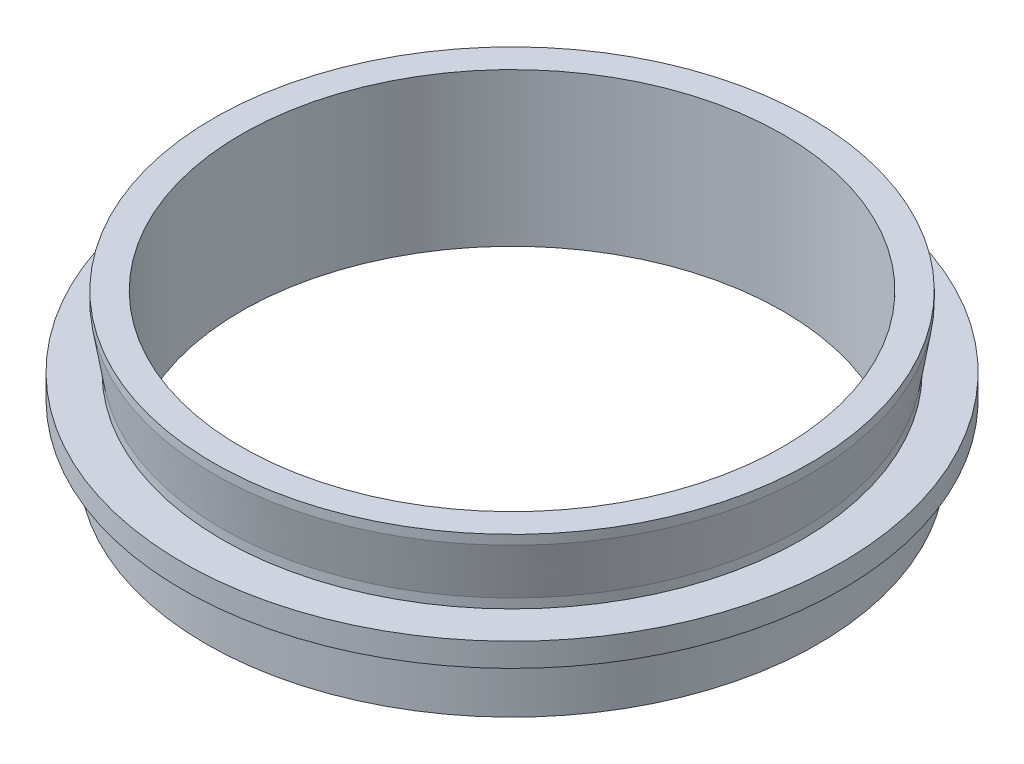
SolidWorks part; units mm, degrees
ref_plane "前视基准面" through (0, 0, 0) normal (0, 0, 1) x (1, 0, 0)
ref_plane "上视基准面" through (0, 0, 0) normal (0, 1, 0) x (1, 0, 0)
ref_plane "右视基准面" through (0, 0, 0) normal (1, 0, 0) x (0, 0, -1)
sketch "草图1" plane through (0, 0, 0) normal (0, 0, 1) x (1, 0, 0)
  line L0 (0, 0) -> (0, 73.2965) construction
  line L1 (-23, 0) -> (-23, 13)
  line L2 (-23, 13) -> (-25.365, 13)
  line L3 (-25.365, 13) -> (-25.365, 12.2)
  line L4 (-25.365, 12.2) -> (-24.635, 7.8)
  line L5 (-24.635, 7.8) -> (-24.635, 7)
  line L6 (-24.635, 7) -> (-28, 7)
  line L7 (-28, 7) -> (-28, 5)
  line L8 (-28, 5) -> (-25.6, 5)
  line L9 (-25.6, 5) -> (-25.6, 4)
  line L10 (-25.6, 4) -> (-26, 4)
  line L11 (-26, 4) -> (-26, 0)
  line L12 (-26, 0) -> (-23, 0)
  point P5 (-24.635, 13.9012)
  dimension "D1" = 23
  dimension "D2" = 25.365
  dimension "D3" = 24.635
  dimension "D4" = 26
  dimension "D5" = 25.6
  dimension "D6" = 13
  dimension "D7" = 6
  dimension "D8" = 2
  dimension "D9" = 1
  dimension "D10" = 0.8
  dimension "D11" = 0.8
  dimension "D12" = 0
  dimension "D13" = 28
revolve "旋转1" add sketch "草图1" angle 360 about L0
cosmetic thread "装饰螺纹线1" parameters "D1"=13, "D2"=47
cosmetic thread "装饰螺纹线2" parameters "D2"=51
